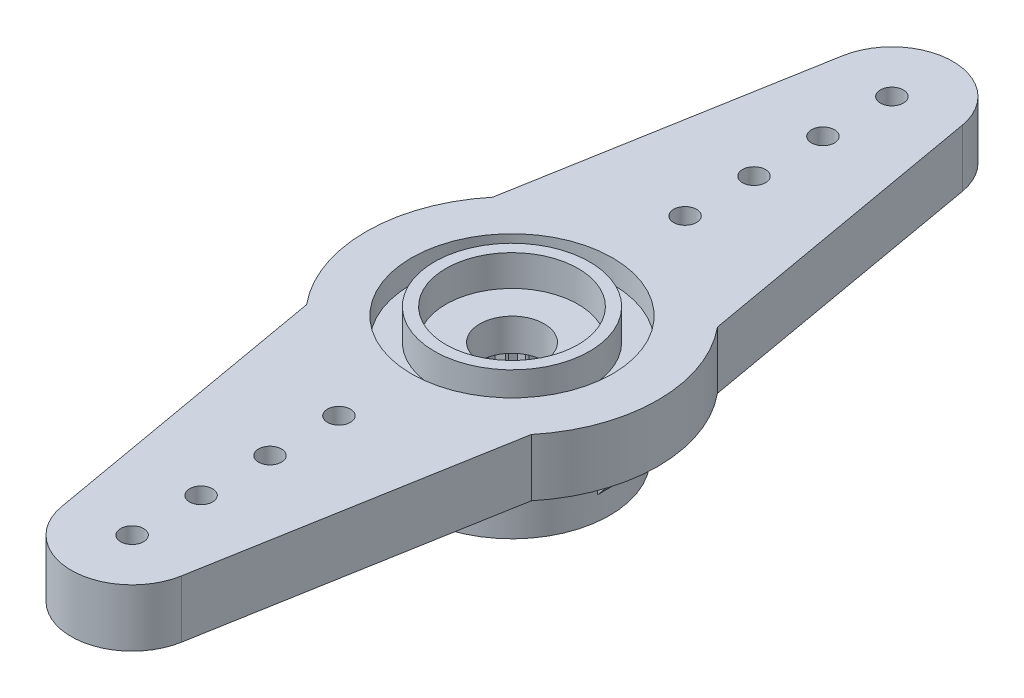
SolidWorks part; units mm, degrees
material "PC High Viscosity"
ref_plane "Front Plane" through (0, 0, 0) normal (0, 0, 1) x (1, 0, 0)
ref_plane "Top Plane" through (0, 0, 0) normal (0, 1, 0) x (1, 0, 0)
ref_plane "Right Plane" through (0, 0, 0) normal (1, 0, 0) x (0, 0, -1)
sketch "BaseS" plane through (0, 0, 0) normal (0, 1, 0) x (1, 0, 0)
  circle A0 centre (0, 0) radius 6.35
  dimension "D1" = 12.7
extrude "BASE" add sketch "BaseS" along normal blind 5.4
sketch "TopBoreS" plane through (0, 5.4, 0) normal (0, 1, 0) x (1, 0, 0)
  circle A0 centre (0, 0) radius 1.4
  dimension "D1" = 2.8
extrude "TOP BORE" cut sketch "TopBoreS" against normal through all
sketch "HornHalfS" plane through (0, 5.4, 0) normal (0, 1, 0) x (1, 0, 0)
  line L0 (0, 0) -> (0, 16.53) construction
  line L1 (-2.6097, 16.9902) -> (-4.8916, 4.049)
  line L2 (0, 19.18) -> (0, 16.53) construction
  line L3 (2.6097, 16.9902) -> (4.8916, 4.049)
  arc A0 (2.6097, 16.9902) -> (-2.6097, 16.9902) centre (0, 16.53) ccw
  arc A1 (4.8916, 4.049) -> (-4.8916, 4.049) centre (0, 0) ccw
  circle A2 centre (0, 0) radius 6.35 construction
  dimension "D1" = 5.3
  dimension "D2" = 19.18
  dimension "D3" = 10
  dimension "D4" = 9.7832
extrude "HORN HALF" add sketch "HornHalfS" against normal blind 2.5
sketch "HornAttachS" plane through (0, 5.4, 0) normal (0, 1, 0) x (1, 0, 0)
  circle A0 centre (0, 16.53) radius 0.5
  dimension "D1" = 1
extrude "HORN ATTACH" cut sketch "HornAttachS" against normal through all
sketch "HA LP RS" plane through (0, 0, 0) normal (0, 1, 0) x (1, 0, 0)
  line L0 (0, 0) -> (0, 16.53) construction
pattern_linear "HA LP" count 4 spacing 3 along (0, 0, 1) of "HORN ATTACH"
mirror "HORN BODIES" about plane through (0, 0, 0) normal (0, 0, 1) of "HA LP", "HORN ATTACH", "HORN HALF"
sketch "ToothS" plane through (0, 0, 0) normal (0, -1, 0) x (1, 0, 0)
  line L0 (0, -2.9) -> (0.2629, -2.5867)
  line L1 (0, -2.9) -> (-0.2629, -2.5867)
  line L2 (0, -2.6) -> (0, -2.9) construction
  line L3 (0, 0) -> (0, -2.6) construction
  arc A0 (-0.2629, -2.5867) -> (0.2629, -2.5867) centre (0, 0) ccw
  dimension "D1" = 5.2
  dimension "D2" = 80
  dimension "D3" = 0.3
extrude "TOOTH" cut sketch "ToothS" against normal blind 3
pattern_circular "TOOTH CP" count 26 over 360 about axis through (0, 0, 0) along (0, 1, 0) of "TOOTH"
sketch "BottomBoreS" plane through (0, 0, 0) normal (0, -1, 0) x (-1, 0, 0)
  circle A0 centre (0, 0) radius 2.6
  arc A1 (0.2629, 2.5867) -> (-0.2629, 2.5867) centre (0, 0) ccw construction
extrude "BOTTOM BORE" cut sketch "BottomBoreS" against normal up to surface (3 mm away) up to face at (-0.6451, 3, 2.6172)
sketch "HoldingShaftS" plane through (0, 0, 0) normal (0, -1, 0) x (1, 0, 0)
  circle A0 centre (0, 0) radius 6.35 construction
  circle A1 centre (0, 0) radius 6.35
  circle A2 centre (0, 0) radius 4.25
  dimension "D1" = 2.1
  dimension "D2" = 8.5
extrude "HOLDING SHAFT" cut sketch "HoldingShaftS" against normal up to surface (2.9 mm away) up to face at (0, 2.9, -13.03)
sketch "RibS" plane through (0, 0, 0) normal (0, 0, 1) x (1, 0, 0)
  line L0 (4.21, 1) -> (5.8043, 2.9)
  line L1 (5.8043, 2.9) -> (4.21, 2.9)
  line L2 (4.21, 1) -> (4.16, 1)
  line L3 (4.16, 1) -> (4.16, 2.9)
  line L4 (4.21, 1) -> (4.21, 2.9) construction
  line L5 (4.16, 2.9) -> (4.21, 2.9)
  line L6 (-4.25, 2.9) -> (4.25, 2.9) construction
  line L7 (4.21, 2.9) -> (4.25, 2.9) construction
  line L8 (4.25, 0) -> (4.25, 2.9) construction
  point P5 (4.25, 2.9)
  point P13 (4.25, 2.9)
  point P14 (0, 0)
  point P15 (0, 0)
  dimension "D1" = 1.9
  dimension "D2" = 0.05
  dimension "D3" = 40
  dimension "D4" = 0.09
extrude "RIB" add sketch "RibS" along normal mid plane 1
pattern_circular "RIB CP" count 4 over 360 about axis through (0, 0, 0) along (0, 1, 0) of "RIB"
sketch "TopCutS" plane through (0, 5.4, 0) normal (0, 1, 0) x (1, 0, 0)
  circle A0 centre (0, 0) radius 4.375
  arc A1 (4.8916, -4.049) -> (4.8916, 4.049) centre (0, 0) ccw construction
  dimension "D1" = 1.975
  dimension "D2" = 8.75
extrude "TOP CUT" cut sketch "TopCutS" against normal blind 1
sketch "TopPocketCylinderS" plane through (0, 4.4, 0) normal (0, 1, 0) x (1, 0, 0)
  circle A0 centre (0, 0) radius 2.875
  circle A1 centre (0, 0) radius 3.375
  circle A2 centre (0, 0) radius 4.375 construction
  point P3 (1.4, 1.4)
  point P4 (0, 0)
  point P5 (0, 0)
  point P6 (0, 0)
  point P7 (0, 0)
  dimension "D2" = 0.5
  dimension "D1" = 1
  dimension "D3" = 6.75
extrude "TOP POCKET CYLINDER" add sketch "TopPocketCylinderS" along normal offset from surface (1.35 mm away) 0.35 up to face at (0, 5.4, 4.375) offset beyond the face yes
